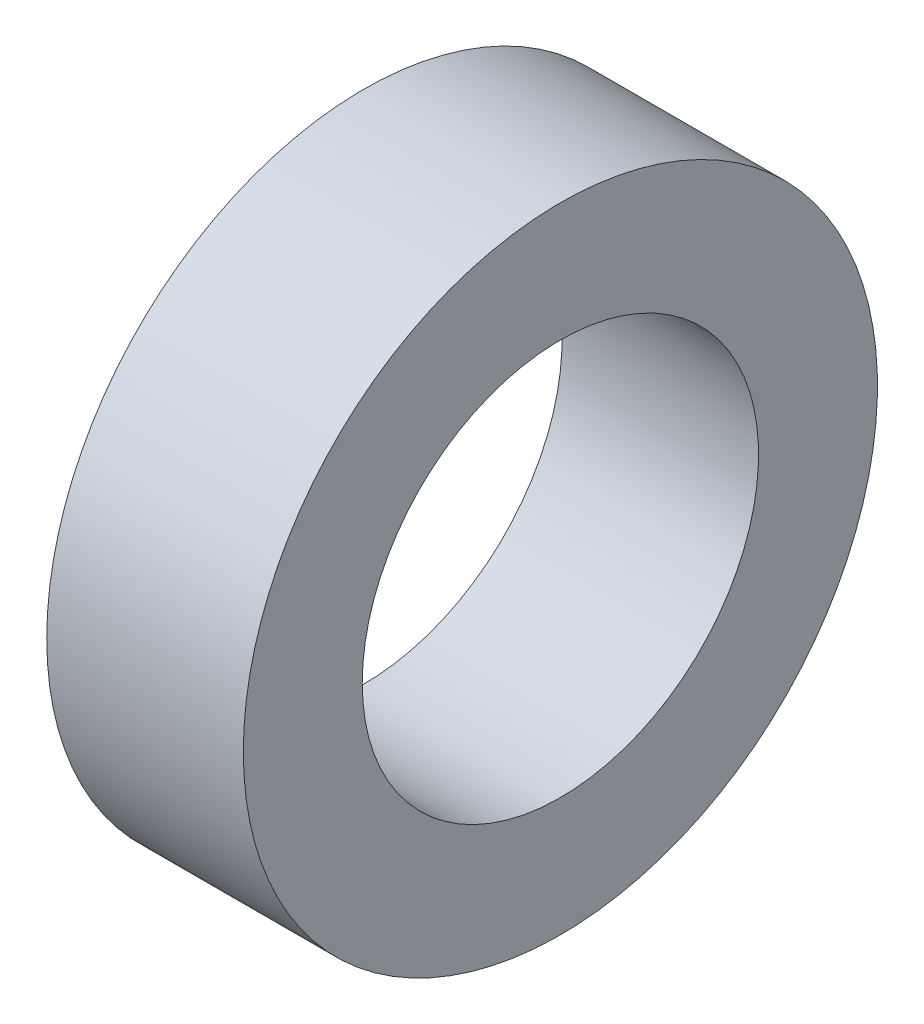
SolidWorks part; units mm, degrees
ref_plane "Front Plane" through (0, 0, 0) normal (0, 0, 1) x (1, 0, 0)
ref_plane "Top Plane" through (0, 0, 0) normal (0, 1, 0) x (1, 0, 0)
ref_plane "Right Plane" through (0, 0, 0) normal (1, 0, 0) x (0, 0, -1)
sketch "Sketch2" plane through (0, 0, 0) normal (0, 0, 1) x (1, 0, 0)
  line L0 (0, 0) -> (58.591, 0) construction
  line L2 (0, 0) -> (18.4, 0)
  line L3 (0, 0) -> (0, 2.5)
  line L4 (0, 2.5) -> (18.4, 2.5)
  line L5 (18.4, 0) -> (18.4, 2.5)
  line L6 (6.0094, 2.5) -> (6.0094, 6)
  line L11 (6.0094, 6) -> (9.9794, 6)
  line L16 (12.9794, 6) -> (12.9794, 3)
  line L17 (12.9794, 3) -> (13.6398, 3)
  line L18 (13.6398, 3) -> (13.6398, 2.5)
  line L19 (13.6398, 2.5) -> (6.0094, 2.5)
  line L22 (13.6398, 2.5) -> (16.1198, 2.5)
  line L23 (13.6398, 2.5) -> (13.6398, 4)
  line L24 (13.6398, 4) -> (16.1198, 4)
  line L25 (16.1198, 2.5) -> (16.1198, 4)
  line L27 (6.0094, 6) -> (9.9794, 6)
  line L28 (6.0094, 6) -> (6.0094, 9)
  line L29 (6.0094, 9) -> (9.9794, 9)
  line L30 (9.9794, 6) -> (9.9794, 9)
  line L31 (6.0094, 9) -> (6.0094, 8.25)
  line L32 (6.0094, 8.25) -> (5.0094, 8.25)
  line L33 (8.6609, 22.001) -> (8.6609, 12.476) construction
  line L34 (5.0094, 12.476) -> (12.3124, 12.476)
  line L35 (9.9794, 9) -> (12.3124, 9)
  line L36 (5.0094, 7.9375) -> (1.7709, 7.9375)
  line L37 (5.0094, 8.25) -> (5.0094, 12.476)
  line L38 (5.0094, 7.9375) -> (5.0094, 13.9365)
  line L39 (5.0094, 13.9365) -> (1.7709, 13.9365)
  line L40 (1.7709, 7.9375) -> (1.7709, 13.9365)
  line L41 (5.0094, 22.001) -> (12.3124, 22.001)
  line L42 (5.0094, 22.001) -> (5.0094, 30.1625)
  line L43 (5.0094, 30.1625) -> (12.3124, 30.1625)
  line L44 (12.3124, 22.001) -> (12.3124, 30.1625)
  line L49 (16.6398, 22.001) -> (16.6398, 7.5)
  line L51 (23.0198, 7.5) -> (23.0198, 6.5)
  line L54 (16.1198, 4) -> (13.6398, 4)
  line L56 (18.0398, 7.5) -> (23.0198, 7.5)
  line L57 (13.3124, 22.001) -> (16.6398, 22.001)
  line L58 (16.1198, 3.5) -> (20.0198, 3.5)
  line L59 (29.9098, 14) -> (26.9098, 11)
  line L60 (4.0094, 31.75) -> (18.0398, 31.75)
  line L61 (18.0398, 7.5) -> (23.0198, 7.5)
  line L62 (18.0398, 7.5) -> (18.0398, 12)
  line L63 (18.0398, 12) -> (23.0198, 12)
  line L64 (23.0198, 7.5) -> (23.0198, 12)
  line L65 (18.0398, 31.75) -> (18.0398, 12)
  line L66 (23.0198, 11) -> (26.9098, 11)
  line L67 (34.8098, 23) -> (31.3098, 19.5)
  line L68 (35.8098, 31) -> (38.7998, 33.99)
  line L69 (29.9098, 14) -> (29.9098, 15)
  line L70 (29.9098, 15) -> (22.9398, 15)
  line L71 (22.9398, 15) -> (21.0398, 15)
  line L72 (18.0398, 7.5) -> (16.6398, 7.5)
  line L73 (21.0398, 15) -> (21.0398, 43)
  line L74 (19.6115, 40) -> (9.6516, 40)
  line L75 (9.6516, 40) -> (4.0094, 40)
  line L76 (21.0398, 43) -> (19.6115, 43)
  line L77 (22.9398, 15) -> (29.9098, 15)
  line L78 (22.9398, 15) -> (22.9398, 21)
  line L79 (22.9398, 21) -> (29.9098, 21)
  line L80 (29.9098, 15) -> (29.9098, 21)
  line L81 (9.6516, 40) -> (19.6115, 40)
  line L82 (9.6516, 40) -> (9.6516, 50)
  line L83 (9.6516, 50) -> (19.6115, 50)
  line L84 (19.6115, 40) -> (19.6115, 50)
  line L85 (4.0094, 40) -> (4.0094, 31.75)
  line L86 (12.9794, 3) -> (12.9794, 2.5)
  line L87 (31.3098, 19.5) -> (29.9098, 19.5)
  line L88 (21.4694, 63.5) -> (21.4694, 51.308)
  line L89 (21.4694, 63.5) -> (25.9398, 63.5)
  line L90 (25.9398, 63.5) -> (25.9398, 25)
  line L91 (27.8398, 25) -> (25.9398, 25)
  line L92 (9.6516, 48) -> (8.2233, 48)
  line L93 (8.2233, 48) -> (8.2233, 53.476)
  line L94 (8.2233, 53.476) -> (19.6115, 53.476)
  line L95 (19.6115, 53.476) -> (19.6115, 50)
  line L96 (13.9174, 63.001) -> (13.9174, 53.476) construction
  line L97 (8.2233, 63.001) -> (19.6115, 63.001)
  line L98 (8.2233, 63.001) -> (8.2233, 68.2625)
  line L99 (8.2233, 68.2625) -> (19.6115, 68.2625)
  line L100 (19.6115, 63.001) -> (19.6115, 68.2625)
  line L101 (12.9794, 6) -> (11.9794, 6)
  line L102 (8.2233, 44.825) -> (4.9848, 44.825)
  line L103 (8.2233, 44.825) -> (8.2233, 54.9365)
  line L104 (8.2233, 54.9365) -> (4.9848, 54.9365)
  line L106 (9.9794, 6) -> (10.8794, 6)
  line L107 (27.8398, 25) -> (34.8098, 25)
  line L108 (34.8098, 25) -> (34.8098, 23)
  line L109 (0, 0) -> (-2, 0)
  line L110 (0, 0) -> (0, 11)
  line L111 (27.8398, 25) -> (34.8098, 25)
  line L112 (27.8398, 25) -> (27.8398, 32.5)
  line L113 (27.8398, 32.5) -> (34.8098, 32.5)
  line L114 (34.8098, 25) -> (34.8098, 32.5)
  line L115 (35.8098, 31) -> (34.8098, 31)
  line L116 (27.8398, 32.5) -> (27.8398, 64.5)
  line L117 (20.5849, 74.025) -> (6.2499, 74.025)
  line L118 (6.2499, 74.025) -> (6.2499, 76.2)
  line L119 (38.7998, 47.29) -> (30.8398, 55.25)
  line L120 (0, 11) -> (-2, 11)
  line L121 (38.7998, 43.815) -> (30.8623, 43.815)
  line L123 (-4.8152, 69.85) -> (1.5348, 76.2)
  line L124 (38.7998, 47.29) -> (38.7998, 33.99)
  line L125 (-2, 0) -> (-2, 11)
  line L126 (38.7998, 37.465) -> (30.8623, 37.465)
  line L127 (30.8623, 43.815) -> (30.8623, 37.465)
  line L128 (6.0094, 2.5) -> (6.0094, 0)
  line L129 (-0.0152, 63.5) -> (-0.0152, 30)
  line L132 (4.9848, 63.5) -> (-0.0152, 63.5)
  line L136 (-1.8152, 30) -> (-11.7752, 30)
  line L138 (-13.7752, 25.4) -> (-2, 25.4)
  line L139 (-2, 25.4) -> (-2, 11.5)
  line L140 (27.8398, 64.5) -> (20.5849, 64.5)
  line L141 (-1.8152, 30) -> (-11.7752, 30)
  line L142 (-1.8152, 30) -> (-1.8152, 39)
  line L143 (-1.8152, 39) -> (-11.7752, 39)
  line L144 (-11.7752, 30) -> (-11.7752, 39)
  line L145 (20.5849, 64.5) -> (20.5849, 74.025)
  line L146 (-12.7752, 37) -> (-12.7752, 47.29)
  line L147 (-12.7752, 37) -> (-11.7752, 37)
  line L148 (30.8398, 55.25) -> (30.8398, 76.2)
  line L149 (11.9794, 6) -> (11.9794, 5.45)
  line L154 (-2, 11.5) -> (0.5, 11.5)
  line L155 (4.9848, 60.6197) -> (24.0348, 60.6197)
  line L160 (4.9848, 60.6197) -> (4.9848, 55.8572)
  line L161 (4.9848, 55.8572) -> (24.0348, 55.8572)
  line L166 (24.0348, 60.6197) -> (24.0348, 55.8572)
  line L167 (4.9848, 60.6197) -> (24.0348, 55.8572) construction
  line L172 (4.9848, 55.8572) -> (24.0348, 60.6197) construction
  line L173 (24.0348, 62.2072) -> (25.9398, 62.2072)
  line L174 (11.9794, 5.45) -> (10.8794, 5.45)
  line L175 (10.8794, 6) -> (10.8794, 5.45)
  line L176 (24.0348, 62.2072) -> (24.0348, 54.2697)
  line L177 (24.0348, 54.2697) -> (25.9398, 54.2697)
  line L178 (25.9398, 62.2072) -> (25.9398, 54.2697)
  line L179 (24.0348, 62.2072) -> (25.9398, 54.2697) construction
  line L180 (24.0348, 54.2697) -> (25.9398, 62.2072) construction
  line L181 (3, 19.6197) -> (15.7, 19.6197)
  line L182 (3, 19.6197) -> (3, 14.8572)
  line L183 (3, 14.8572) -> (15.7, 14.8572)
  line L184 (15.7, 19.6197) -> (15.7, 14.8572)
  line L185 (3, 19.6197) -> (15.7, 14.8572) construction
  line L186 (3, 14.8572) -> (15.7, 19.6197) construction
  line L187 (15.7, 21.2072) -> (16.6398, 21.2072)
  line L188 (15.7, 21.2072) -> (15.7, 13.2697)
  line L189 (15.7, 13.2697) -> (16.6398, 13.2697)
  line L190 (16.6398, 21.2072) -> (16.6398, 13.2697)
  line L191 (15.7, 21.2072) -> (16.6398, 13.2697) construction
  line L192 (15.7, 13.2697) -> (16.6398, 21.2072) construction
  line L193 (0.5, 11.5) -> (0.5, 6.9375)
  line L194 (0.5, 6.9375) -> (1.7709, 6.9375)
  line L195 (23.0198, 6.5) -> (20.0198, 3.5)
  line L196 (4.9848, 63.5) -> (4.9848, 54.9365)
  line L197 (3, 43.825) -> (4.9848, 43.825)
  line L198 (1.7709, 6.9375) -> (1.7709, 7.9375)
  line L199 (6.0094, 0) -> (12.9794, 0)
  line L200 (12.9794, 0) -> (12.9794, 2.5)
  line L201 (18.0398, 31.75) -> (18.0398, 35.875)
  line L202 (18.0398, 35.875) -> (21.0398, 35.875)
  line L203 (30.8398, 76.2) -> (6.2499, 76.2)
  line L204 (2.8049, 69.85) -> (7.2499, 69.85) construction
  line L205 (7.2499, 67.4688) -> (26.2999, 67.4688)
  line L206 (7.2499, 74.025) -> (7.2499, 64.5)
  line L207 (7.2499, 64.5) -> (-1.8152, 64.5)
  line L208 (-1.8152, 64.5) -> (-1.8152, 39)
  line L209 (-12.7752, 47.29) -> (-4.8152, 55.25)
  line L210 (-4.8152, 55.25) -> (-4.8152, 69.85)
  line L211 (7.2499, 67.4688) -> (7.2499, 72.2312)
  line L212 (7.2499, 72.2312) -> (26.2999, 72.2313)
  line L213 (26.2999, 67.4688) -> (26.2999, 72.2313)
  line L214 (26.2999, 73.8187) -> (30.8398, 73.8187)
  line L215 (26.2999, 73.8187) -> (26.2999, 65.8813)
  line L216 (26.2999, 65.8813) -> (30.8398, 65.8813)
  line L217 (30.8398, 73.8187) -> (30.8398, 65.8813)
  line L218 (2.8049, 72.2313) -> (25.0299, 72.2313)
  line L219 (2.8049, 72.2313) -> (2.8049, 67.4687)
  line L220 (2.8049, 67.4687) -> (25.0299, 67.4687)
  line L221 (25.0299, 72.2313) -> (25.0299, 67.4687)
  line L222 (25.0299, 69.85) -> (20.5849, 69.85) construction
  line L223 (21.4694, 51.308) -> (22.9398, 51.308)
  line L224 (22.9398, 51.308) -> (22.9398, 21)
  line L225 (13.6398, 4) -> (13.6398, 12.2697)
  line L226 (13.6398, 12.2697) -> (13.3124, 12.2697)
  line L227 (13.3124, 12.2697) -> (13.3124, 22.001)
  line L228 (12.3124, 9) -> (12.3124, 12.476)
  line L229 (-1.8152, 30) -> (-0.0152, 30)
  line L230 (8.2233, 65.6317) -> (2.8049, 65.6317) construction
  line L231 (19.6115, 65.6317) -> (25.0299, 65.6317) construction
  line L232 (1.5348, 76.2) -> (6.2499, 76.2)
  line L233 (-11.7752, 30) -> (-13.7752, 30)
  line L234 (-13.7752, 30) -> (-13.7752, 25.4)
  line L235 (3, 13.9365) -> (3, 43.825)
  line L236 (4.9848, 54.9365) -> (4.9848, 44.825)
  line L237 (4.9848, 43.825) -> (4.9848, 44.825)
  circle A0 centre (26.8898, 25.95) radius 0.95
  circle A1 centre (21.9898, 15.95) radius 0.95
  circle A2 centre (17.3398, 8.2) radius 0.7
  circle A3 centre (10.4294, 6.45) radius 0.45
  circle A4 centre (-0.9152, 30.9) radius 0.9
  point P7 (24.9873, 58.2385)
  point P131 (16.1699, 17.2385)
  point P135 (14.5098, 58.2385)
  point P146 (9.35, 17.2385)
sketch "Sketch3" plane through (0, 0, 0) normal (0, 0, 1) x (1, 0, 0)
  line L0 (0, 2.5) -> (18.4, 2.5) construction
  line L1 (16.1198, 2.5) -> (16.1198, 4) construction
  line L2 (13.6398, 4) -> (16.1198, 4) construction
  line L3 (13.6398, 2.5) -> (13.6398, 4) construction
  line L4 (13.6398, 2.5) -> (16.1198, 2.5)
  line L5 (16.1198, 2.5) -> (16.1198, 4)
  line L6 (13.6398, 4) -> (16.1198, 4)
  line L7 (13.6398, 2.5) -> (13.6398, 4)
revolve "Revolve1" add sketch "Sketch3" angle 360 about L0
